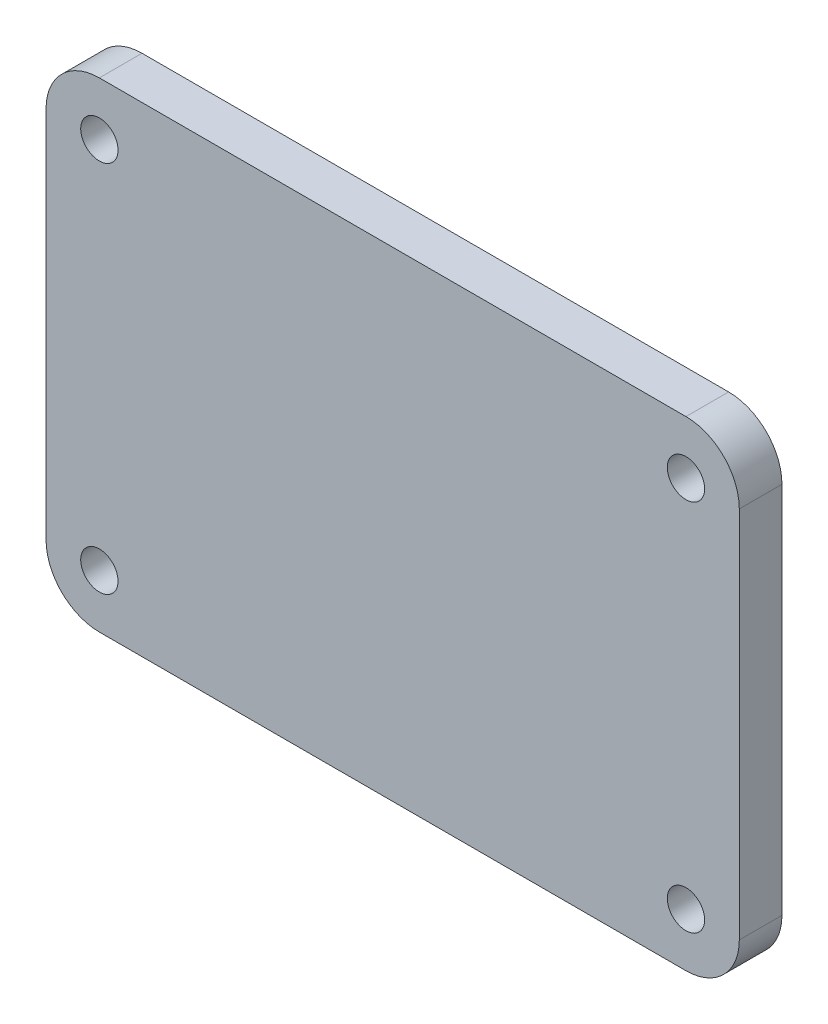
SolidWorks part; units mm, degrees
material "有机玻璃"
ref_plane "前视基准面" through (0, 0, 0) normal (0, 0, 1) x (1, 0, 0)
ref_plane "上视基准面" through (0, 0, 0) normal (0, 1, 0) x (1, 0, 0)
ref_plane "右视基准面" through (0, 0, 0) normal (1, 0, 0) x (0, 0, -1)
sketch "草图1" plane through (0, 0, 0) normal (0, 0, 1) x (1, 0, 0)
  line L1 (-32.5, -22.5) -> (32.5, -22.5)
  line L2 (-32.5, -22.5) -> (-32.5, 22.5)
  line L3 (-32.5, 22.5) -> (32.5, 22.5)
  line L4 (32.5, -22.5) -> (32.5, 22.5)
  line L5 (-32.5, -22.5) -> (32.5, 22.5) construction
  line L6 (-32.5, 22.5) -> (32.5, -22.5) construction
  point P0 (0, 0)
  dimension "D1" = 65
  dimension "D2" = 45
extrude "凸台-拉伸1" add sketch "草图1" along normal blind 4
hole_wizard "Ø3.5 (3.5) 直径孔1" positions "草图3" profile "草图2" hole size "Ø3.5" standard "GB" end condition through all
sketch "草图3" plane through (0, 0, 4) normal (0, 0, 1) x (1, 0, 0)
  line L0 (-32.5, 0) -> (32.5, 0) construction
  line L1 (-32.5, 22.5) -> (-32.5, -22.5) construction
  line L2 (32.5, -22.5) -> (32.5, 22.5) construction
  line L4 (0, 22.5) -> (0, -22.5) construction
  line L5 (32.5, 22.5) -> (-32.5, 22.5) construction
  line L6 (-32.5, -22.5) -> (32.5, -22.5) construction
  point P0 (-27.5, 17.5)
  point P2 (-27.5, -17.5)
  point P4 (27.5, 17.5)
  point P6 (27.5, -17.5)
  dimension "D1" = 35
  dimension "D2" = 55
sketch "草图2" plane through (-27.5, 17.5, 4) normal (1, 0, 0) x (0, -1, 0)
  line L0 (0, 0) -> (0, 4)
  line L1 (0, 4) -> (1.75, 4)
  line L2 (1.75, 4) -> (1.75, 0)
  line L5 (1.75, 0) -> (0, 0)
  line L11 (0, -6.35) -> (0, 107.95) construction
  dimension "通孔孔直径" = 3.5
  dimension "通孔孔深度" = 4
fillet "圆角1" radius 5 4 edges at (-32.5, -22.5, 2) (-32.5, 22.5, 2) (32.5, -22.5, 2) (32.5, 22.5, 2)
